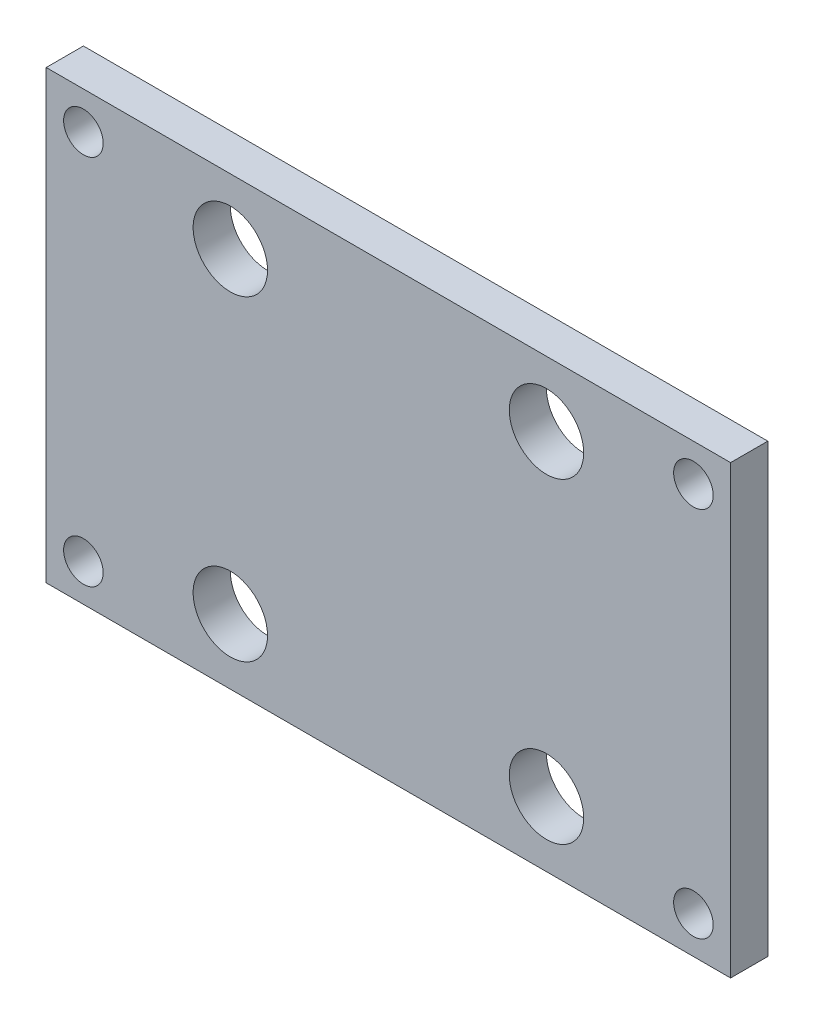
SolidWorks part; units mm, degrees
material "Plain Carbon Steel"
ref_plane "Front Plane" through (0, 0, 0) normal (0, 0, 1) x (1, 0, 0)
ref_plane "Top Plane" through (0, 0, 0) normal (0, 1, 0) x (1, 0, 0)
ref_plane "Right Plane" through (0, 0, 0) normal (1, 0, 0) x (0, 0, -1)
sketch "Sketch1" plane through (0, 0, 0) normal (0, 0, 1) x (1, 0, 0)
  line L1 (-58.42, -38.1) -> (58.42, -38.1)
  line L2 (-58.42, -38.1) -> (-58.42, 38.1)
  line L3 (-58.42, 38.1) -> (58.42, 38.1)
  line L4 (58.42, -38.1) -> (58.42, 38.1)
  line L5 (-58.42, -38.1) -> (58.42, 38.1) construction
  line L6 (-58.42, 38.1) -> (58.42, -38.1) construction
  point P0 (0, 0)
  dimension "D1" = 76.2
  dimension "D2" = 116.84
extrude "Extrude1" add sketch "Sketch1" along normal blind 6.35
sketch "Sketch2" plane through (0, 0, 6.35) normal (0, 0, 1) x (1, 0, 0)
  line L0 (-58.42, 31.75) -> (-52.07, 31.75) construction
  line L1 (-58.42, 38.1) -> (-58.42, -38.1) construction
  line L2 (58.42, 38.1) -> (-58.42, 38.1) construction
  dimension "D1" = 6.35
  dimension "D2" = 6.35
hole_wizard "1/4 Clearance Hole1" positions "3DSketch1" profile "Sketch4" hole size "1/4" standard "Ansi Inch" end condition through all
sketch3d "3DSketch1"
  point P0 (-52.07, 31.75, 6.35)
sketch "Sketch4" plane through (-52.07, 31.75, 6.35) normal (1, 0, 0) x (0, -1, 0)
  line L0 (0, 0) -> (0, 6.35)
  line L1 (0, 6.35) -> (3.3782, 6.35)
  line L2 (3.3782, 6.35) -> (3.3782, 0)
  line L5 (3.3782, 0) -> (0, 0)
  line L11 (0, -6.35) -> (0, 107.95) construction
  dimension "Thru Hole Dia." = 6.7564
  dimension "Thru Hole Depth" = 6.35
mirror "Mirror1" about plane through (0, 0, 0) normal (0, 1, 0) of "1/4 Clearance Hole1"
mirror "Mirror2" about plane through (0, 0, 0) normal (1, 0, 0) of "Mirror1", "1/4 Clearance Hole1"
sketch "Sketch5" plane through (0, 0, 6.35) normal (0, 0, 1) x (1, 0, 0)
  line L1 (-26.9875, -26.9875) -> (26.9875, -26.9875)
  line L2 (-26.9875, -26.9875) -> (-26.9875, 26.9875)
  line L3 (-26.9875, 26.9875) -> (26.9875, 26.9875)
  line L4 (26.9875, -26.9875) -> (26.9875, 26.9875)
  line L5 (-26.9875, -26.9875) -> (26.9875, 26.9875) construction
  line L6 (-26.9875, 26.9875) -> (26.9875, -26.9875) construction
  point P1 (0, 0)
  dimension "D1" = 53.975
hole_wizard "1/2 (0.5) Diameter Hole1" positions "3DSketch2" profile "Sketch6" hole size "1/2" standard "Ansi Inch"
sketch3d "3DSketch2"
  point P0 (-26.9875, 26.9875, 6.35)
  point P3 (26.9875, 26.9875, 6.35)
  point P6 (26.9875, -26.9875, 6.35)
  point P9 (-26.9875, -26.9875, 6.35)
sketch "Sketch6" plane through (-26.9875, 26.9875, 6.35) normal (1, 0, 0) x (0, -1, 0)
  line L0 (0, 0) -> (0, 21.5955)
  line L1 (0, 21.5955) -> (6.35, 17.78)
  line L2 (6.35, 17.78) -> (6.35, 0)
  line L5 (6.35, 0) -> (0, 0)
  line L10 (0, 21.5955) -> (-6.35, 17.78) construction
  line L11 (0, -6.35) -> (0, 107.95) construction
  dimension "Hole Dia." = 12.7
  dimension "Hole Depth" = 17.78
  dimension "Drill Angle" = 118
